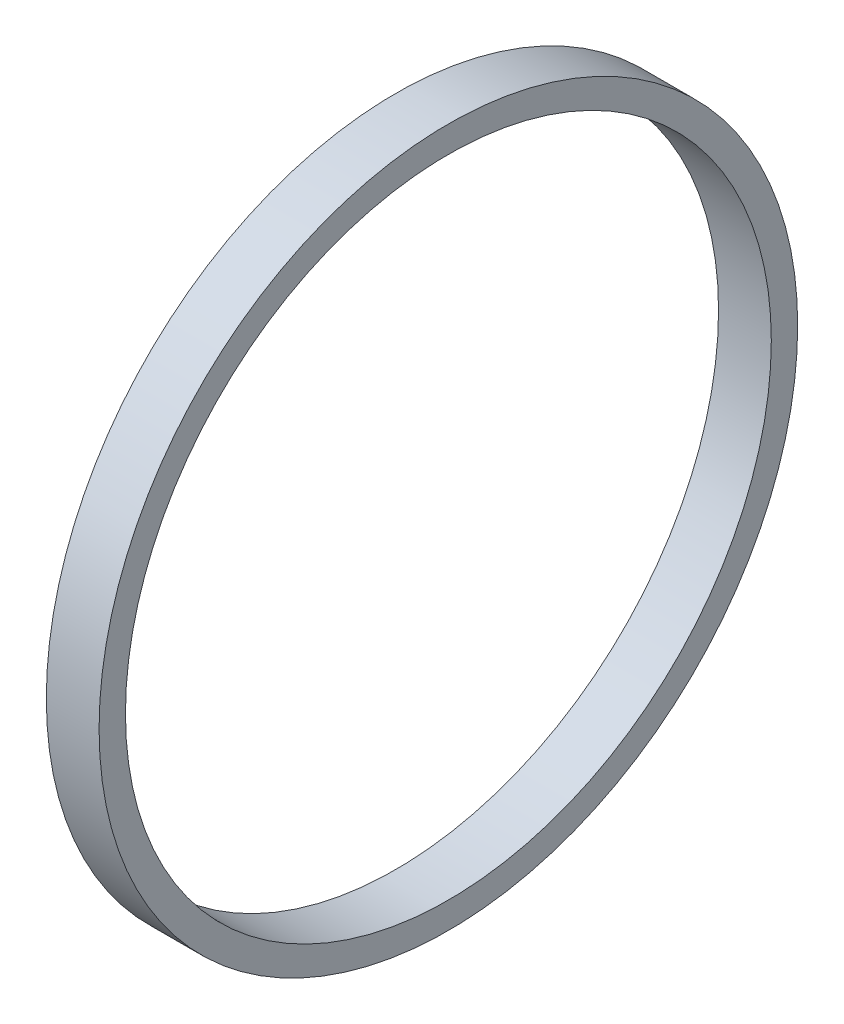
SolidWorks part; units mm, degrees
material "Rubber"
ref_plane "Front Plane" through (0, 0, 0) normal (0, 0, 1) x (1, 0, 0)
ref_plane "Top Plane" through (0, 0, 0) normal (0, 1, 0) x (1, 0, 0)
ref_plane "Right Plane" through (0, 0, 0) normal (1, 0, 0) x (0, 0, -1)
sketch "Sketch1" plane through (0, 0, 0) normal (1, 0, 0) x (0, 0, -1)
  circle A0 centre (0, 0) radius 21.0212
  circle A1 centre (0, 0) radius 19.4337
  dimension "D1" = 42.0424
  dimension "D2" = 1.5875
extrude "Boss-Extrude1" add sketch "Sketch1" along normal blind 3.175
